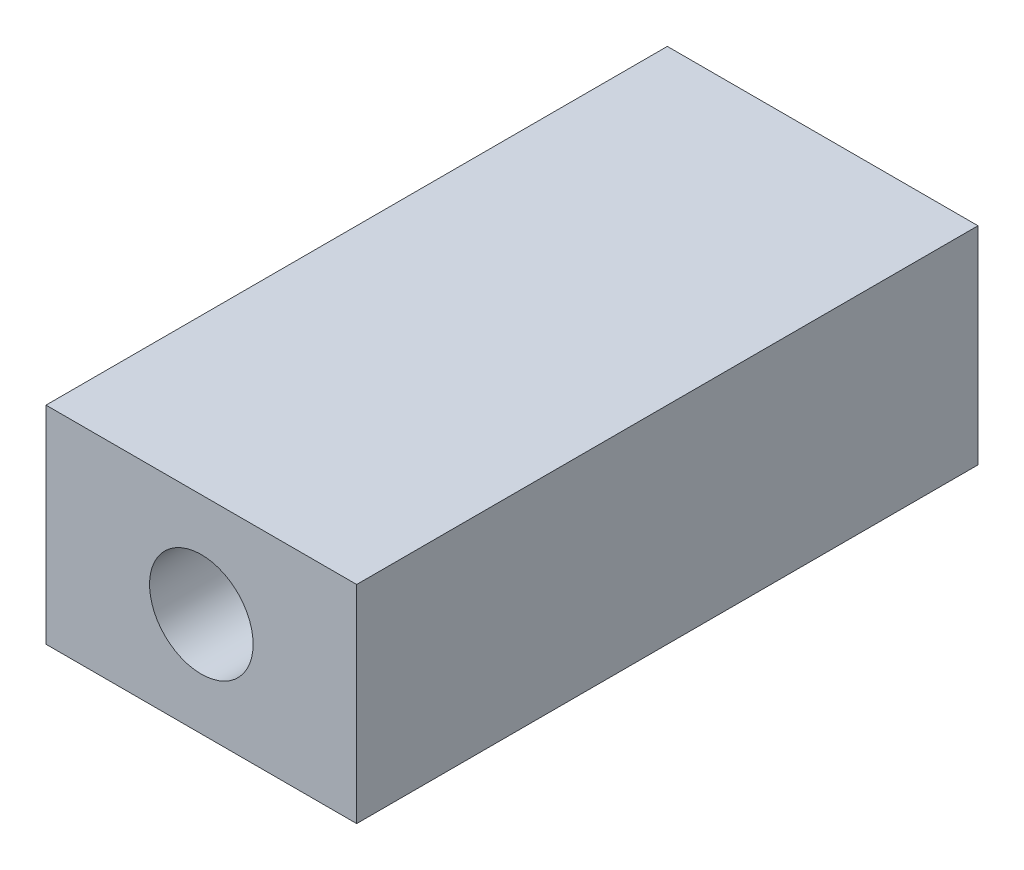
SolidWorks part; units mm, degrees
ref_plane "Plan de face" through (0, 0, 0) normal (0, 0, 1) x (1, 0, 0)
ref_plane "Plan de dessus" through (0, 0, 0) normal (0, 1, 0) x (1, 0, 0)
ref_plane "Plan de droite" through (0, 0, 0) normal (1, 0, 0) x (0, 0, -1)
sketch "Esquisse1" plane through (0, 0, 0) normal (0, 0, 1) x (1, 0, 0)
  line L0 (0.3495, 1.5877) -> (0.3495, -2.4123) construction
  line L1 (-2.6505, 1.5877) -> (3.3495, 1.5877)
  line L2 (-2.6505, 1.5877) -> (-2.6505, -2.4123)
  line L3 (-2.6505, -2.4123) -> (3.3495, -2.4123)
  line L4 (3.3495, 1.5877) -> (3.3495, -2.4123)
  line L5 (-2.6505, -0.4123) -> (3.3495, -0.4123) construction
  circle A0 centre (0.3495, -0.4123) radius 0.5
  dimension "D3" = 1
  dimension "D1" = 6
  dimension "D2" = 4
extrude "Boss.-Extru.1" add sketch "Esquisse1" along normal blind 12
sketch "Esquisse2" plane through (0, 0, 12) normal (0, 0, 1) x (1, 0, 0)
  circle A0 centre (0.3495, -0.4123) radius 1
  dimension "D1" = 2
extrude "Enlèv. mat.-Extru.1" cut sketch "Esquisse2" against normal blind 6
